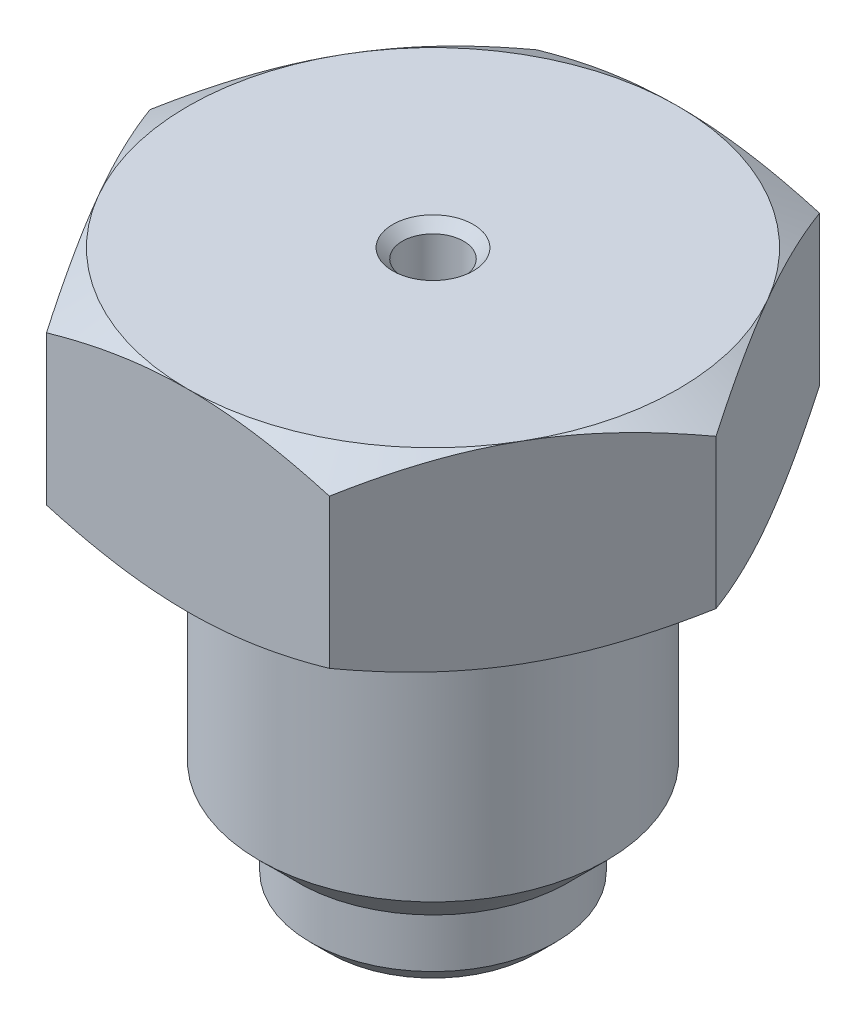
SolidWorks part; units mm, degrees
ref_plane "Alzado" through (0, 0, 0) normal (0, 0, 1) x (1, 0, 0)
ref_plane "Planta" through (0, 0, 0) normal (0, 1, 0) x (1, 0, 0)
ref_plane "Vista lateral" through (0, 0, 0) normal (1, 0, 0) x (0, 0, -1)
sketch "Croquis1" plane through (0, 0, 0) normal (0, 1, 0) x (1, 0, 0)
  line L1 (14.6647, 0) -> (7.3323, 12.7)
  line L2 (7.3323, 12.7) -> (-7.3323, 12.7)
  line L3 (-7.3323, 12.7) -> (-14.6647, 0)
  line L4 (-14.6647, 0) -> (-7.3323, -12.7)
  line L5 (-7.3323, -12.7) -> (7.3323, -12.7)
  line L6 (7.3323, -12.7) -> (14.6647, 0)
  circle A0 centre (0, 0) radius 12.7 construction
  dimension "D1" = 25.4
extrude "Saliente-Extruir3" add sketch "Croquis1" along normal blind 10
sketch "Croquis5" plane through (0, 0, 0) normal (0, -1, 0) x (1, 0, 0)
  circle A0 centre (0, 0) radius 12.7
extrude "Cortar-Extruir4" cut sketch "Croquis5" against normal blind 10 draft 60 flip side to cut
sketch "Croquis6" plane through (0, 10, 0) normal (0, 1, 0) x (1, 0, 0)
  circle A0 centre (0, 0) radius 12.7
extrude "Cortar-Extruir5" cut sketch "Croquis6" against normal blind 10 draft 60 flip side to cut
sketch "Croquis7" plane through (0, 0, 0) normal (0, -1, 0) x (1, 0, 0)
  circle A0 centre (0, 0) radius 9
  dimension "D1" = 18
extrude "Saliente-Extruir4" add sketch "Croquis7" along normal blind 15
chamfer "Chaflán1" distance 2 angle 45 1 edges at (0, -15, -9)
sketch "Croquis8" plane through (0, 10, 0) normal (0, 1, 0) x (1, 0, 0)
  circle A0 centre (0, 0) radius 1.5875
  dimension "3.175" = 3.175
extrude "Cortar-Extruir6" cut sketch "Croquis8" against normal blind 26 from offset 0
chamfer "Chaflán2" distance 0.5 angle 45 1 edges at (0, 10, 1.5875)
sketch "Croquis9" plane through (0, -15, 0) normal (0, -1, 0) x (1, 0, 0)
  circle A0 centre (0, 0) radius 6.35
  dimension "D1" = 12.7
extrude "Saliente-Extruir5" add sketch "Croquis9" along normal blind 4
chamfer "Chaflán4" distance 1 angle 45 1 edges at (0, -19, -6.35)
sketch "Croquis10" plane through (0, -19, 0) normal (0, -1, 0) x (1, 0, 0)
  circle A0 centre (0, 0) radius 1.5875
  dimension "D1" = 3.175
extrude "Cortar-Extruir7" cut sketch "Croquis10" against normal blind 14
